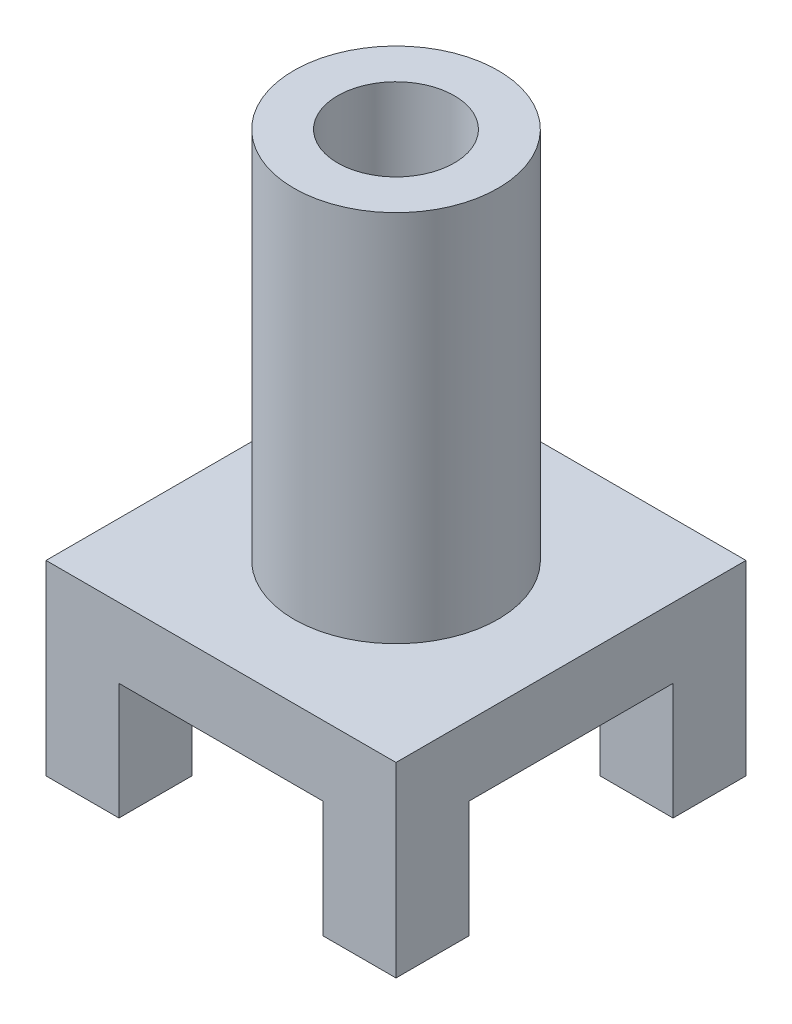
SolidWorks part; units mm, degrees
ref_plane "Front Plane" through (0, 0, 0) normal (0, 0, 1) x (1, 0, 0)
ref_plane "Top Plane" through (0, 0, 0) normal (0, 1, 0) x (1, 0, 0)
ref_plane "Right Plane" through (0, 0, 0) normal (1, 0, 0) x (0, 0, -1)
sketch "Sketch2" plane through (0, 0, 0) normal (0, 1, 0) x (1, 0, 0)
  line L1 (30, -30) -> (-30, -30)
  line L2 (30, -30) -> (30, 30)
  line L3 (30, 30) -> (-30, 30)
  line L4 (-30, -30) -> (-30, 30)
  line L5 (30, -30) -> (-30, 30) construction
  line L6 (30, 30) -> (-30, -30) construction
  point P0 (0, 0)
  dimension "D1" = 60
  dimension "D2" = 60
extrude "Boss-Extrude2" add sketch "Sketch2" along normal blind 32 contours L2 L1 L4 L3
sketch "Sketch3" plane through (0, 0, 30) normal (0, 0, 1) x (1, 0, 0)
  line L0 (30, 0) -> (-30, 0) construction
  line L1 (-17.5, 0) -> (17.5, 0)
  line L2 (-17.5, 0) -> (-17.5, 20)
  line L3 (-17.5, 20) -> (17.5, 20)
  line L4 (17.5, 0) -> (17.5, 20)
  line L5 (-30, 32) -> (-30, 0) construction
  dimension "D1" = 35
  dimension "D2" = 20
  dimension "D3" = 12.5
extrude "Cut-Extrude1" cut sketch "Sketch3" against normal blind 60 contours L2 L1 L4 L3
sketch "Sketch4" plane through (30, 0, 0) normal (1, 0, 0) x (0, 0, -1)
  line L0 (-30, 0) -> (30, 0) construction
  line L1 (17.5, 20) -> (-17.5, 20)
  line L2 (17.5, 20) -> (17.5, 0)
  line L3 (17.5, 0) -> (-17.5, 0)
  line L4 (-17.5, 20) -> (-17.5, 0)
  line L5 (-30, 32) -> (-30, 0) construction
  dimension "D1" = 35
  dimension "D2" = 20
  dimension "D3" = 12.5
extrude "Cut-Extrude2" cut sketch "Sketch4" against normal through all contours L2 L1 L4 L3
sketch "Sketch5" plane through (0, 32, 0) normal (0, 1, 0) x (1, 0, 0)
  circle A0 centre (0, 0) radius 17.5
  dimension "D1" = 35
extrude "Boss-Extrude3" add sketch "Sketch5" along normal blind 64 contours A0
sketch "Sketch6" plane through (0, 96, 0) normal (0, 1, 0) x (1, 0, 0)
  circle A0 centre (0, 0) radius 10
  dimension "D1" = 20
extrude "Cut-Extrude3" cut sketch "Sketch6" against normal through all and the other way through all contours A0
